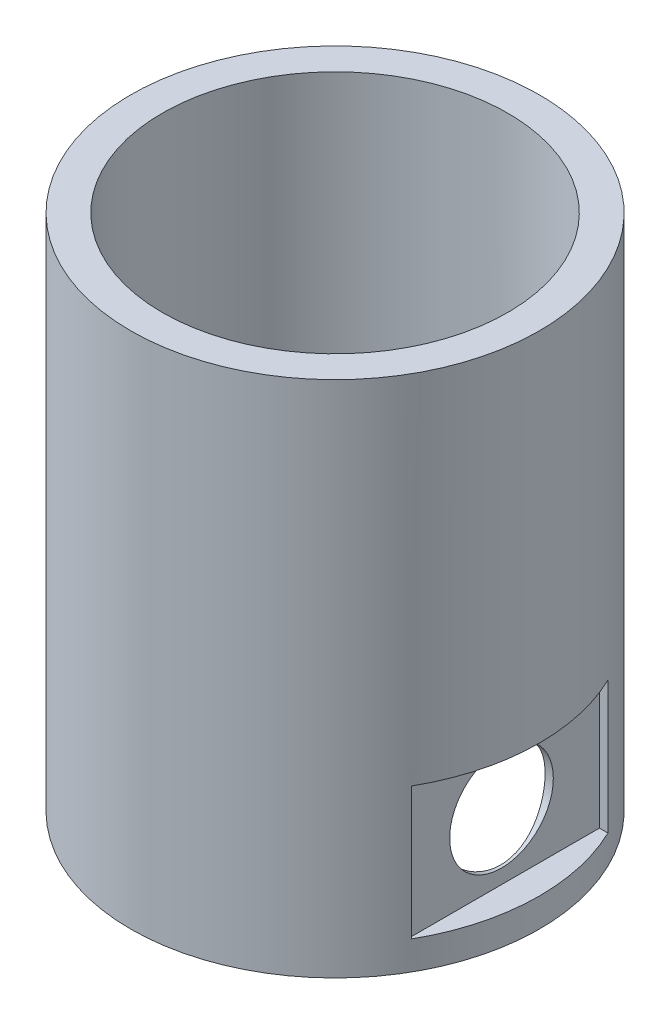
SolidWorks part; units mm, degrees
ref_plane "Front Plane" through (0, 0, 0) normal (0, 0, 1) x (1, 0, 0)
ref_plane "Top Plane" through (0, 0, 0) normal (0, 1, 0) x (1, 0, 0)
ref_plane "Right Plane" through (0, 0, 0) normal (1, 0, 0) x (0, 0, -1)
sketch "Sketch1" plane through (0, 0, 0) normal (0, 1, 0) x (1, 0, 0)
  circle A0 centre (0, 0.545) radius 15
  circle A1 centre (0, 0.545) radius 17.75
  dimension "D1" = 30
  dimension "D2" = 35.5
extrude "Boss-Extrude1" add sketch "Sketch1" along normal blind 45
ref_plane "Plane1" through (17.75, 0, 0) normal (1, 0, 0) x (0, 0, -1)
sketch "Sketch2" plane through (17.75, 0, 0) normal (1, 0, 0) x (0, 0, -1)
  line L0 (0, 0) -> (0, 59.5498) construction
  line L1 (-8.25, 13.9931) -> (8.25, 13.9931)
  line L2 (-8.25, 13.9931) -> (-8.25, 2.4931)
  line L3 (-8.25, 2.4931) -> (8.25, 2.4931)
  line L4 (8.25, 13.9931) -> (8.25, 2.4931)
  dimension "D1" = 16.5
  dimension "D2" = 11.5
extrude "Cut-Extrude1" cut sketch "Sketch2" against normal blind 2.5
sketch "Sketch3" plane through (15.25, 0, 0) normal (1, 0, 0) x (0, 0, -1)
  line L0 (-8.25, 13.9931) -> (-8.25, 2.4931) construction
  line L1 (-16.2217, 8.2431) -> (15.3392, 8.2431) construction
  line L2 (-28.4001, 13.9931) -> (34.6789, 13.9931) construction
  line L3 (-29.901, 2.4931) -> (36.2655, 2.4931) construction
  line L4 (-8.25, 2.4931) -> (8.25, 2.4931) construction
  line L5 (8.25, 13.9931) -> (-8.25, 13.9931) construction
  circle A0 centre (-0.25, 8.2431) radius 4.5
  point P14 (0, 0)
  dimension "D1" = 9
  dimension "D2" = 8
  dimension "D3" = 5.75
  dimension "D4" = 5.75
extrude "Cut-Extrude2" cut sketch "Sketch3" against normal up to next
pattern_circular "CirPattern1" count 2 over 90 about axis through (0, 0, -0.545) along (0, 1, 0) of "Cut-Extrude1", "Cut-Extrude2"
